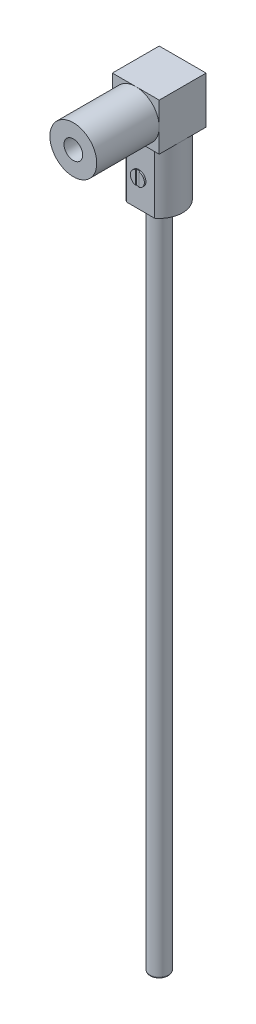
SolidWorks part; units mm, degrees
ref_plane "Front" through (0, 0, 0) normal (0, 0, 1) x (1, 0, 0)
ref_plane "Top" through (0, 0, 0) normal (0, 1, 0) x (1, 0, 0)
ref_plane "Right" through (0, 0, 0) normal (1, 0, 0) x (0, 0, -1)
sketch "Sketch3" plane through (0, 0, 0) normal (0, 0, 1) x (1, 0, 0)
  line L1 (0, 0) -> (30, 0)
  line L2 (0, 0) -> (0, 30)
  line L3 (0, 30) -> (30, 30)
  line L4 (30, 0) -> (30, 30)
  dimension "D1" = 30
  dimension "D2" = 30
extrude "Boss-Extrude1" add sketch "Sketch3" along normal blind 30
sketch "Sketch4" plane through (0, 0, 30) normal (0, 0, 1) x (1, 0, 0)
  line L0 (30, 0) -> (30, 30) construction
  line L1 (0, 30) -> (0, 0) construction
  line L2 (30, 30) -> (0, 30) construction
  line L3 (0, 0) -> (30, 0) construction
  circle A0 centre (15, 15) radius 15
  circle A1 centre (15, 15) radius 6
  dimension "D1" = 12
extrude "Boss-Extrude2" add sketch "Sketch4" along normal blind 40
sketch "Sketch5" plane through (0, 0, 0) normal (0, -1, 0) x (1, 0, 0)
  line L0 (0, 30) -> (0, 0) construction
  line L2 (0, 0) -> (30, 0) construction
  circle A0 centre (15, 15) radius 15
  dimension "D1" = 30
extrude "Boss-Extrude3" add sketch "Sketch5" along normal blind 40
sketch "Sketch6" plane through (0, -40, 0) normal (0, -1, 0) x (1, 0, 0)
  line L0 (6, 27) -> (24, 27)
  circle A0 centre (15, 15) radius 15 construction
  arc A1 (24, 27) -> (6, 27) centre (15, 15) ccw
  dimension "D1" = 27
extrude "Cut-Extrude4" cut sketch "Sketch6" against normal blind 40
sketch "Sketch7" plane through (0, 0, 27) normal (0, 0, 1) x (1, 0, 0)
  line L1 (6, -40) -> (24, -40) construction
  circle A0 centre (15, -21.5) radius 3
  dimension "D1" = 6
  dimension "D2" = 18.5
extrude "Boss-Extrude4" add sketch "Sketch7" along normal blind 1
sketch "Sketch8" plane through (0, 0, 28) normal (0, 0, 1) x (1, 0, 0)
  circle A0 centre (15, -21.5) radius 4.5
  dimension "D1" = 9
extrude "Boss-Extrude5" add sketch "Sketch8" along normal blind 1
sketch "Sketch9" plane through (0, 0, 29) normal (0, 0, 1) x (1, 0, 0)
  line L0 (15, -14.1432) -> (15, -28.8457) construction
  line L1 (16.2, -17.163) -> (16.2, -25.837)
  line L2 (13.8, -17.163) -> (13.8, -25.837)
  circle A0 centre (15, -21.5) radius 4.5 construction
  arc A1 (13.8, -25.837) -> (16.2, -25.837) centre (15, -21.5) ccw
  arc A2 (16.2, -17.163) -> (13.8, -17.163) centre (15, -21.5) ccw
  dimension "D1" = 1.2
extrude "Cut-Extrude5" cut sketch "Sketch9" against normal blind 0.5
sketch "Sketch10" plane through (0, -40, 0) normal (0, -1, 0) x (1, 0, 0)
  circle A0 centre (15, 15) radius 6
  dimension "D1" = 12
extrude "Boss-Extrude6" add sketch "Sketch10" along normal blind 428
fillet "Fillet1" radius 1 1 edges at (15, -468, 9)
